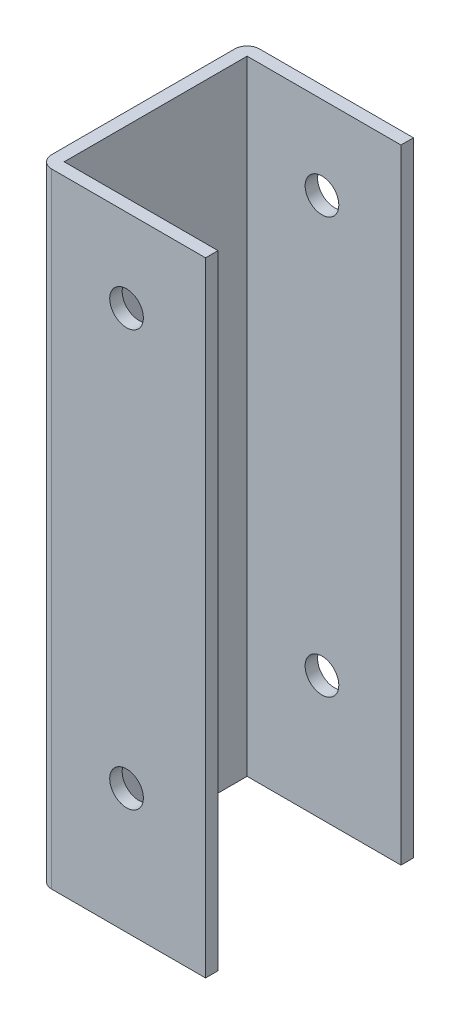
SolidWorks part; units mm, degrees
ref_plane "Спереди" through (0, 0, 0) normal (0, 0, 1) x (1, 0, 0)
ref_plane "Сверху" through (0, 0, 0) normal (0, 1, 0) x (1, 0, 0)
ref_plane "Справа" through (0, 0, 0) normal (1, 0, 0) x (0, 0, -1)
sketch "Эскиз1" plane through (0, 0, 0) normal (0, 1, 0) x (1, 0, 0)
  line L1 (-37, 25) -> (37, 25)
  line L2 (-40, 22) -> (-40, -22)
  line L3 (-37, -25) -> (37, -25)
  line L4 (40, 22) -> (40, -22)
  line L5 (-40, 25) -> (40, -25) construction
  line L6 (-40, -25) -> (40, 25) construction
  arc A0 (-37, 25) -> (-40, 22) centre (-37, 22) ccw
  arc A1 (-40, -22) -> (-37, -25) centre (-37, -22) ccw
  arc A2 (37, -25) -> (40, -22) centre (37, -22) ccw
  arc A3 (37, 25) -> (40, 22) centre (37, 22) cw
  point P0 (0, 0)
  dimension "D1" = 3
extrude "Вытянуть-Тонкостенный1" add sketch "Эскиз1" along normal blind 150 thin
sketch "Эскиз2" plane through (0, 150, 0) normal (0, 1, 0) x (1, 0, 0)
  line L1 (0, -27.4206) -> (41.1465, -27.4206)
  line L2 (0, -27.4206) -> (0, 30.9728)
  line L3 (0, 30.9728) -> (41.1465, 30.9728)
  line L4 (41.1465, -27.4206) -> (41.1465, 30.9728)
extrude "Вырез-Вытянуть1" cut sketch "Эскиз2" against normal through all
sketch "Эскиз3" plane through (0, 0, -25) normal (0, 0, -1) x (-1, 0, 0)
  circle A0 centre (19, 130) radius 4.05
  circle A1 centre (19, 30) radius 4.05
  dimension "D1" = 2
extrude "Вырез-Вытянуть2" cut sketch "Эскиз3" against normal through all
